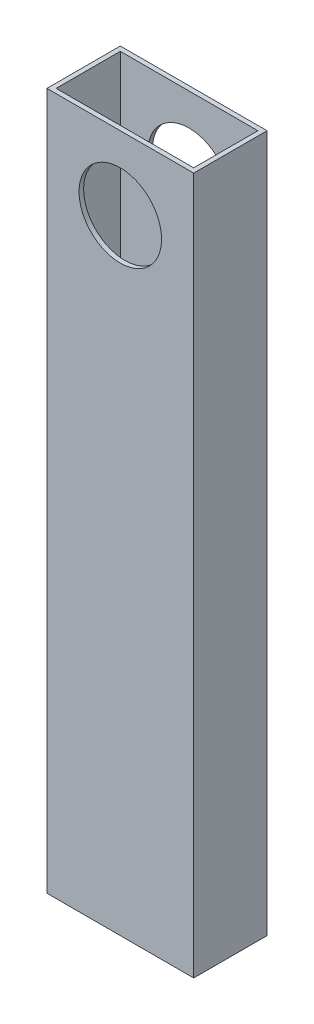
SolidWorks part; units mm, degrees
ref_plane "Front Plane" through (0, 0, 0) normal (0, 0, 1) x (1, 0, 0)
ref_plane "Top Plane" through (0, 0, 0) normal (0, 1, 0) x (1, 0, 0)
ref_plane "Right Plane" through (0, 0, 0) normal (1, 0, 0) x (0, 0, -1)
sketch "Sketch1" plane through (0, 0, 0) normal (0, 1, 0) x (1, 0, 0)
  line L1 (-15.24, 5.0482) -> (35.56, 5.0482)
  line L2 (-15.24, 5.0482) -> (-15.24, -20.3518)
  line L3 (-15.24, -20.3518) -> (35.56, -20.3518)
  line L4 (35.56, 5.0482) -> (35.56, -20.3518)
  line L5 (-13.6525, 3.4607) -> (33.9725, 3.4607)
  line L6 (-13.6525, 3.4607) -> (-13.6525, -18.7643)
  line L7 (-13.6525, -18.7643) -> (33.9725, -18.7643)
  line L8 (33.9725, 3.4607) -> (33.9725, -18.7643)
  dimension "D1" = 1.5875
  dimension "D2" = 1.5875
  dimension "D3" = 1.5875
  dimension "D4" = 1.5875
  dimension "D5" = 50.8
  dimension "D6" = 25.4
extrude "Boss-Extrude1" add sketch "Sketch1" along normal blind 241.3
sketch "Sketch2" plane through (0, 0, -5.0482) normal (0, 0, -1) x (-1, 0, 0)
  line L0 (15.24, 241.3) -> (15.24, 0) construction
  line L1 (-35.56, 241.3) -> (15.24, 241.3) construction
  circle A0 centre (-10.16, 215.9) radius 14.2881
  dimension "D1" = 25.4
  dimension "D2" = 25.4
extrude "Cut-Extrude1" cut sketch "Sketch2" against normal through all
